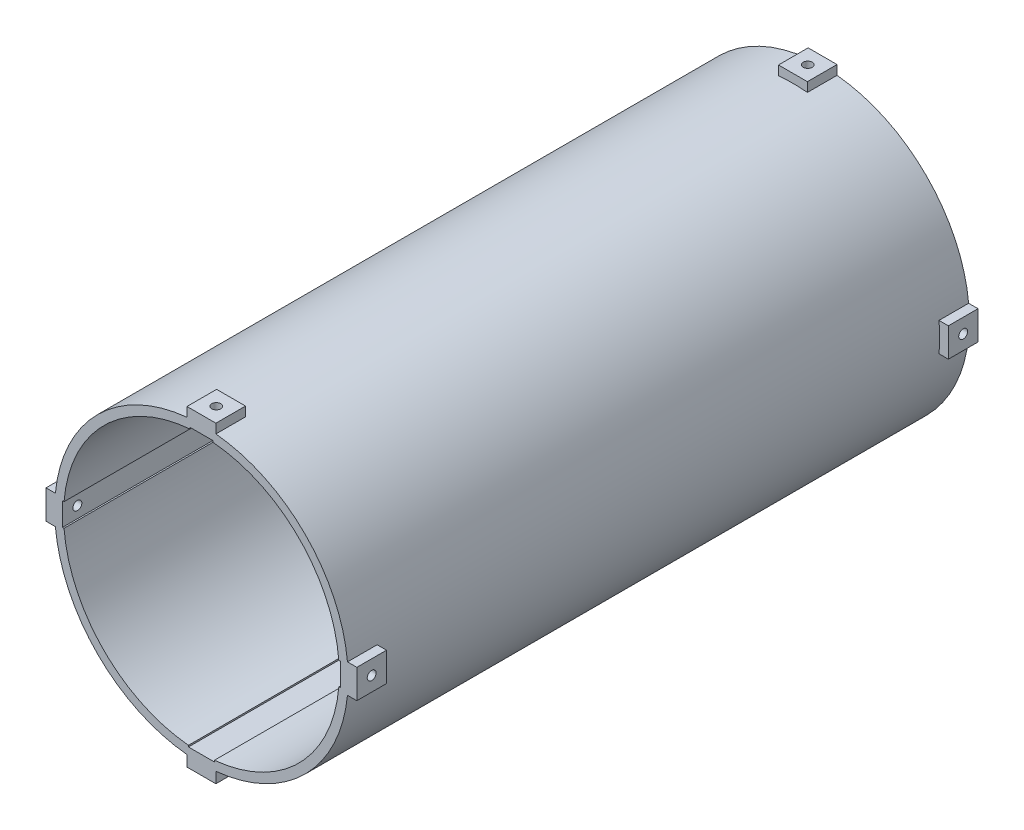
SolidWorks part; units mm, degrees
material "尼龙 101"
ref_plane "前视基准面" through (0, 0, 0) normal (0, 0, 1) x (1, 0, 0)
ref_plane "上视基准面" through (0, 0, 0) normal (0, 1, 0) x (1, 0, 0)
ref_plane "右视基准面" through (0, 0, 0) normal (1, 0, 0) x (0, 0, -1)
other "Configuration Table"
sketch "草图1" plane through (0, 0, 0) normal (0, 0, 1) x (1, 0, 0)
  line L2 (-9.75, -98.5187) -> (-9.75, -105.8352)
  line L3 (-9.75, -105.8352) -> (9.75, -105.8352)
  line L4 (9.75, -98.5187) -> (9.75, -105.8352)
  line L6 (9.75, 98.5187) -> (9.75, 104.8352)
  line L7 (9.75, 104.8352) -> (-9.75, 104.8352)
  line L8 (-9.75, 98.5187) -> (-9.75, 104.8352)
  line L9 (98.5187, 9.75) -> (104.8352, 9.75)
  line L11 (98.5187, -9.75) -> (104.8352, -9.75)
  line L12 (104.8352, 9.75) -> (104.8352, -9.75)
  line L13 (-98.5187, 9.75) -> (-104.8352, 9.75)
  line L15 (-98.5187, -9.75) -> (-104.8352, -9.75)
  line L16 (-104.8352, 9.75) -> (-104.8352, -9.75)
  circle A0 centre (0, 0) radius 102.5 construction
  arc A1 (9.75, -98.5187) -> (98.5187, -9.75) centre (0, 0) ccw
  arc A2 (-98.5187, -9.75) -> (-9.75, -98.5187) centre (0, 0) ccw
  arc A3 (98.5187, 9.75) -> (9.75, 98.5187) centre (0, 0) ccw
  arc A4 (-9.75, 98.5187) -> (-98.5187, 9.75) centre (0, 0) ccw
  point P8 (9.75, -102.0352)
  point P21 (9.75, 102.0352)
  point P22 (-102.0352, -9.75)
  point P25 (102.0352, -9.75)
  dimension "D1" = 205
  dimension "D2" = 198
  dimension "D3" = 19.5
  dimension "D4" = 3.8
  dimension "D5" = 19.5
  dimension "D6" = 2.8
  dimension "D7" = 19.5
  dimension "D8" = 19.5
  dimension "D9" = 2.8
  dimension "D10" = 2.8
extrude "凸台-拉伸1" add sketch "草图1" along normal blind 419
sketch "草图2" plane through (0, 0, 419) normal (0, 0, 1) x (1, 0, 0)
  circle A0 centre (0, 0) radius 99
  arc A1 (-9.75, 98.5187) -> (-98.5187, 9.75) centre (0, 0) ccw construction
  circle A2 centre (0, 0) radius 119
  dimension "D1" = 20
extrude "切除-拉伸1" cut sketch "草图2" against normal offset from surface (379 mm away) 20 from offset 20 up to face at (0, -0.125, 0) offset against normal yes
sketch "草图3" plane through (0, 0, 419) normal (0, 0, 1) x (1, 0, 0)
  circle A0 centre (0, 0) radius 93
  arc A1 (-9.75, 98.5187) -> (-98.5187, 9.75) centre (0, 0) ccw construction
  dimension "D1" = 6
extrude "切除-拉伸2" cut sketch "草图3" against normal through all
sketch "草图4" plane through (0, 0, 419) normal (0, 0, 1) x (1, 0, 0)
  line L1 (-8.75, -92.5875) -> (8.75, -92.5875)
  line L2 (-8.75, -92.5875) -> (-8.75, -93.5875)
  line L3 (-8.75, -93.5875) -> (8.75, -93.5875)
  line L4 (8.75, -92.5875) -> (8.75, -93.5875)
  line L5 (-9.75, -98.5187) -> (-9.75, -105.8352) construction
  line L6 (-98.5187, 9.75) -> (-104.8352, 9.75) construction
  line L7 (-92.6765, 7.75) -> (-93.6765, 7.75)
  line L8 (-92.6765, 7.75) -> (-92.6765, -7.75)
  line L9 (-92.6765, -7.75) -> (-93.6765, -7.75)
  line L10 (-93.6765, 7.75) -> (-93.6765, -7.75)
  line L11 (9.75, 98.5187) -> (9.75, 104.8352) construction
  line L12 (-7.75, 92.6765) -> (7.75, 92.6765)
  line L13 (-7.75, 92.6765) -> (-7.75, 93.6765)
  line L14 (-7.75, 93.6765) -> (7.75, 93.6765)
  line L15 (7.75, 92.6765) -> (7.75, 93.6765)
  line L16 (104.8352, 9.75) -> (98.5187, 9.75) construction
  line L17 (92.6765, 7.75) -> (93.6765, 7.75)
  line L18 (92.6765, 7.75) -> (92.6765, -7.75)
  line L19 (92.6765, -7.75) -> (93.6765, -7.75)
  line L20 (93.6765, 7.75) -> (93.6765, -7.75)
  circle A0 centre (0, 0) radius 93 construction
  dimension "D1" = 1
  dimension "D2" = 1
  dimension "D3" = 2
  dimension "D4" = 1
  dimension "D5" = 1
  dimension "D6" = 2
  dimension "D7" = 2
  dimension "D8" = 1
extrude "切除-拉伸3" cut sketch "草图4" against normal through all
sketch "草图5" plane through (-93.6765, 0, 0) normal (1, 0, 0) x (0, 0, -1)
  line L0 (-419, 7.75) -> (-419, -7.75) construction
  line L1 (0, 7.75) -> (0, -7.75) construction
  circle A0 centre (-409, 0) radius 3
  circle A1 centre (-10, 0) radius 3
  point P4 (-419, 0)
  point P10 (0, 0)
  dimension "D2" = 6
  dimension "D4" = 6
  dimension "D1" = 10
  dimension "D3" = 10
extrude "切除-拉伸4" cut sketch "草图5" against normal through all
sketch "草图6" plane through (0, 0, 0) normal (0, 1, 0) x (1, 0, 0)
  line L0 (0, -1000) -> (0, 49000) construction
pattern_circular "阵列(圆周)1" count 4 every 90 about axis through (0, 0, 1000) along (0, 0, -1) of "切除-拉伸4"
